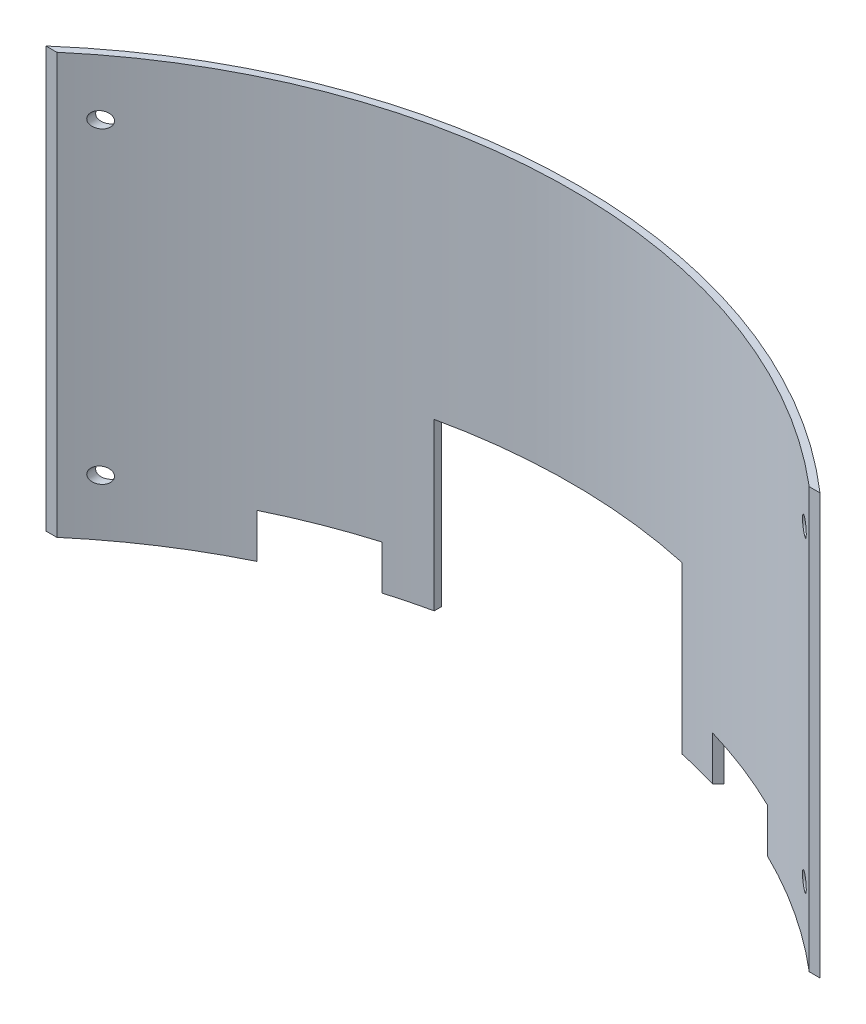
SolidWorks part; units mm, degrees
ref_plane "Front Plane" through (0, 0, 0) normal (0, 0, 1) x (1, 0, 0)
ref_plane "Top Plane" through (0, 0, 0) normal (0, 1, 0) x (1, 0, 0)
ref_plane "Right Plane" through (0, 0, 0) normal (1, 0, 0) x (0, 0, -1)
sketch "Sketch1" plane through (0, 0, 0) normal (0, 1, 0) x (1, 0, 0)
  line L0 (-170.1396, 0) -> (170.1396, 0) construction
  line L7 (170.1396, 0) -> (175, 0)
  line L17 (-175, 0) -> (-170.1396, 0)
  arc A2 (175, 0) -> (-175, 0) centre (0, -200.0147) ccw
  arc A3 (170.1396, 0) -> (-170.1396, 0) centre (0, -200.0147) ccw
  point P0 (0, 65.75)
  point P2 (0, 0)
  dimension "D2" = 3.175
  dimension "D3" = 65.75
  dimension "D1" = 350
extrude "Curved Plate" add sketch "Sketch1" along normal blind 190
sketch "Sketch2" plane through (0, 0, 0) normal (0, 1, 0) x (1, 0, 0)
  line L0 (0, 64.9964) -> (20, 64.9964) construction
  line L1 (-117.7623, 38.235) -> (-105.5219, 25.9946)
  line L2 (-105.5219, 25.9946) -> (-77.2377, 54.2789) construction
  line L3 (-175, 0) -> (-170.1396, 0) construction
  line L4 (-20, 64.9964) -> (-77.2377, 64.9964) construction
  line L5 (-77.2377, 64.9964) -> (-77.2377, 54.2789) construction
  line L6 (-117.7623, 38.235) -> (-175, 38.235) construction
  line L7 (-175, 38.235) -> (-175, 0) construction
  line L8 (0, 0) -> (0, 64.9964) construction
  line L11 (-77.2377, 54.2789) -> (-105.5219, 25.9946) construction
  line L12 (-77.2377, 54.2789) -> (-73.7021, 50.7433)
  line L13 (-105.5219, 25.9946) -> (-101.9864, 22.4591)
  line L14 (-73.7021, 50.7433) -> (-101.9864, 22.4591)
  line L19 (77.2377, 54.2789) -> (73.7021, 50.7433)
  line L20 (73.7021, 50.7433) -> (101.9864, 22.4591)
  line L21 (105.5219, 25.9946) -> (101.9864, 22.4591)
  line L22 (117.7623, 38.235) -> (105.5219, 25.9946)
  line L23 (-20, 64.9964) -> (0, 64.9964) construction
  line L24 (0, 64.9964) -> (20, 64.9964) construction
  line L28 (-20, 64.9964) -> (0, 64.9964) construction
  line L29 (0, 64.9964) -> (0, 65.75) construction
  line L30 (-20, 64.9964) -> (20, 64.9964) construction
  arc A0 (-117.7623, 38.235) -> (-77.2377, 54.2789) centre (0, -200.0147) cw
  arc A1 (175, 0) -> (-175, 0) centre (0, -200.0147) ccw construction
  arc A2 (117.7623, 38.235) -> (77.2377, 54.2789) centre (0, -200.0147) ccw
  arc A4 (-175, 0) -> (-117.7623, 38.235) centre (0, -200.0147) cw construction
  arc A5 (-77.2377, 54.2789) -> (-20, 64.9964) centre (0, -200.0147) cw construction
  arc A6 (-20, 64.9964) -> (20, 64.9964) centre (0, -200.0147) cw construction
  arc A7 (20, 64.9964) -> (77.2377, 54.2789) centre (0, -200.0147) cw construction
  arc A9 (117.7623, 38.235) -> (175, 0) centre (0, -200.0147) cw construction
  point P24 (0, 65.75)
  dimension "D1" = 40
  dimension "D2" = 135
  dimension "D3" = 40
  dimension "D4" = 5
extrude "IR Cutout" cut sketch "Sketch2" along normal blind 20
sketch "Sketch3" plane through (0, 0, 0) normal (0, 0, 1) x (1, 0, 0)
  line L0 (-74.6881, 0) -> (74.6881, 0) construction
  line L1 (-56, 0) -> (56, 0)
  line L2 (-56, 0) -> (-56, 75)
  line L3 (-56, 75) -> (56, 75)
  line L4 (56, 0) -> (56, 75)
  line L5 (0, 75) -> (0, 0) construction
  dimension "D1" = 112
  dimension "D2" = 75
extrude "ChargerBox Cutout" cut sketch "Sketch3" against normal up to surface (59.7831 mm away)
sketch "Sketch5" plane through (0, 0, 0) normal (0, 0, 1) x (1, 0, 0)
  line L0 (166.3349, 190) -> (-166.3349, 190) construction
  line L1 (0, 190) -> (0, 0) construction
  line L2 (-175, 190) -> (-175, 0) construction
  line L3 (-175, 190) -> (-146.425, 190) construction
  line L4 (-175, 0) -> (-146.425, 0) construction
  circle A0 centre (-159.125, 164.6) radius 3.5687
  circle A1 centre (-159.125, 25.4) radius 3.5687
  circle A2 centre (159.125, 25.4) radius 3.5687
  circle A3 centre (159.125, 164.6) radius 3.5687
  dimension "D4" = 7.1374
  dimension "D1" = 15.875
  dimension "D2" = 25.4
  dimension "D3" = 25.4
extrude "Mounting Holes" cut sketch "Sketch5" against normal through all
